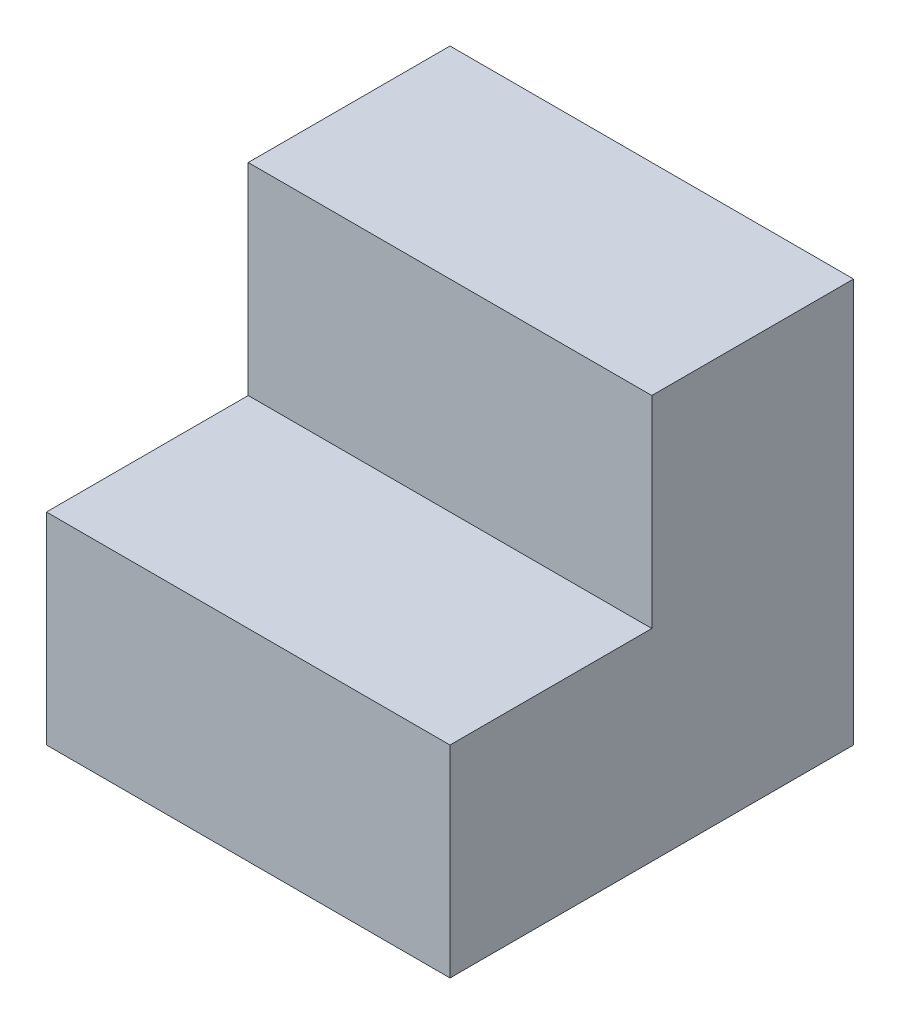
SolidWorks part; units mm, degrees
ref_plane "Front Plane" through (0, 0, 0) normal (0, 0, 1) x (1, 0, 0)
ref_plane "Top Plane" through (0, 0, 0) normal (0, 1, 0) x (1, 0, 0)
ref_plane "Right Plane" through (0, 0, 0) normal (1, 0, 0) x (0, 0, -1)
sketch "Sketch1" plane through (0, 0, 0) normal (1, 0, 0) x (0, 0, -1)
  line L0 (0, 0) -> (0, 30)
  line L1 (0, 30) -> (-15, 30)
  line L2 (-15, 30) -> (-15, 15)
  line L3 (-15, 15) -> (-30, 15)
  line L4 (-30, 15) -> (-30, 0)
  line L5 (-30, 0) -> (0, 0)
  dimension "D1" = 30
  dimension "D2" = 30
  dimension "D3" = 15
  dimension "D4" = 15
extrude "Boss-Extrude1" add sketch "Sketch1" along normal mid plane 30
